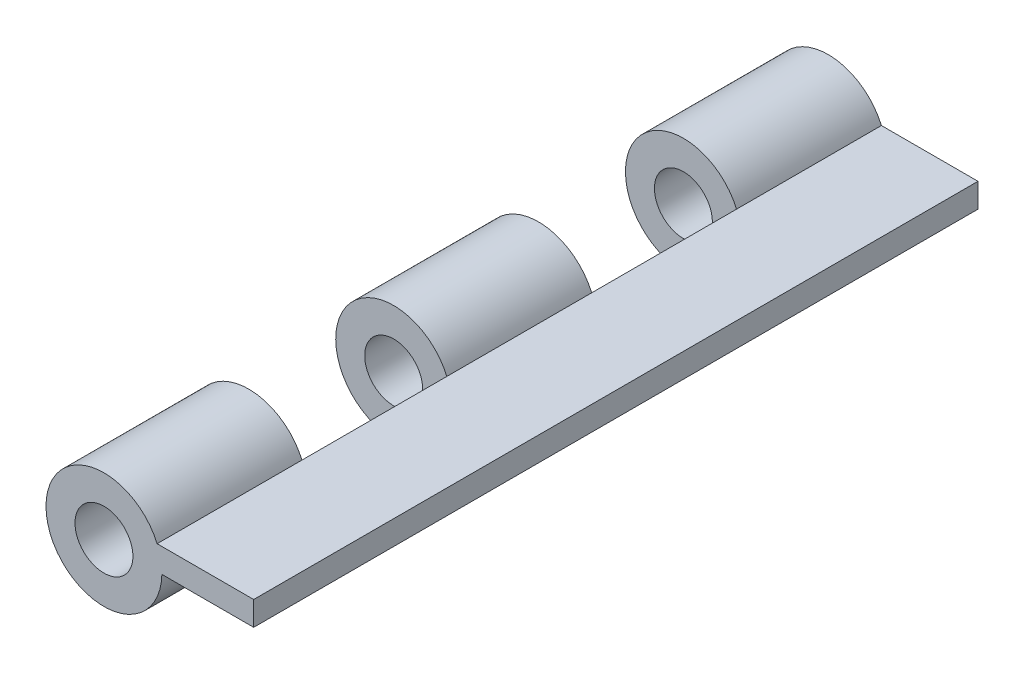
SolidWorks part; units mm, degrees
ref_plane "Front Plane" through (0, 0, 0) normal (0, 0, 1) x (1, 0, 0)
ref_plane "Top Plane" through (0, 0, 0) normal (0, 1, 0) x (1, 0, 0)
ref_plane "Right Plane" through (0, 0, 0) normal (1, 0, 0) x (0, 0, -1)
sketch "Sketch1" plane through (0, 0, 0) normal (0, 1, 0) x (1, 0, 0)
  line L5 (10, -75) -> (-10, -75)
  line L6 (10, -75) -> (10, 75)
  line L7 (10, 75) -> (-10, 75)
  line L8 (-10, -75) -> (-10, 75)
  line L9 (10, -75) -> (-10, 75) construction
  line L10 (10, 75) -> (-10, -75) construction
  point P0 (0, 0)
  dimension "D1" = 150
  dimension "D2" = 20
extrude "Boss-Extrude1" add sketch "Sketch1" along normal mid plane 5
sketch "Sketch5" plane through (0, 0, 75) normal (0, 0, 1) x (1, 0, 0)
  circle A0 centre (-21.0096, -2.2736) radius 12
  circle A1 centre (-21.0096, -2.2736) radius 6
  dimension "D1" = 24
  dimension "D2" = 12
extrude "Boss-Extrude2" add sketch "Sketch5" against normal blind 30
pattern_linear "LPattern1" count 3 spacing 60 along (0, 0, -1) of "Boss-Extrude2"
